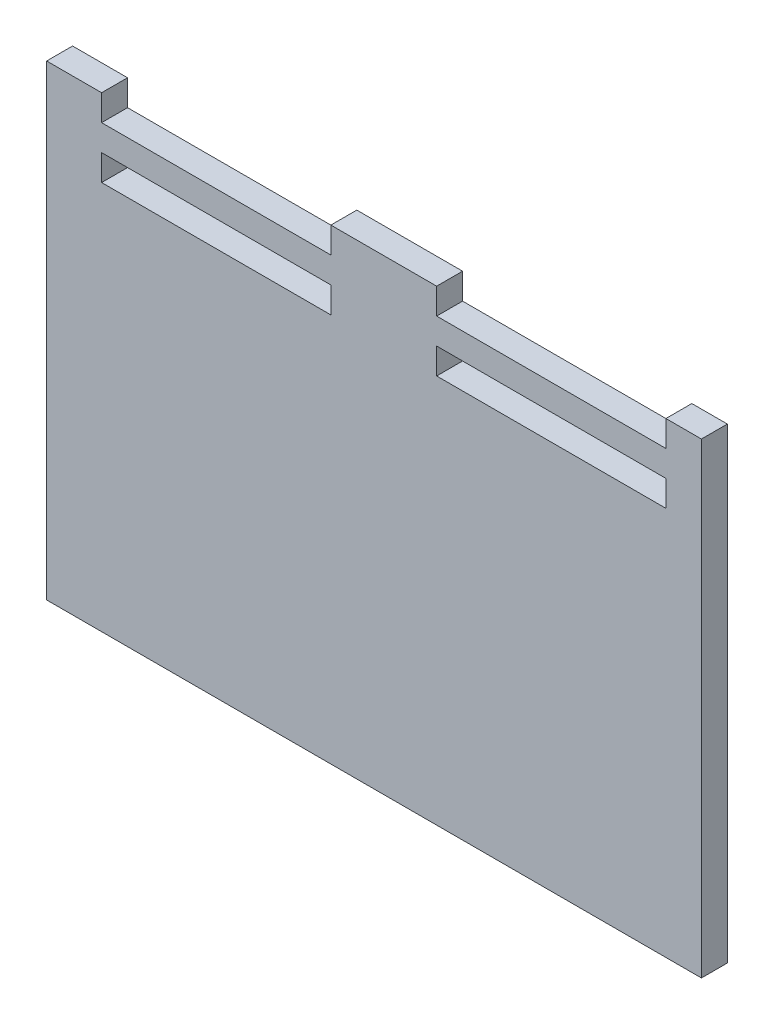
SolidWorks part; units mm, degrees
ref_plane "Front Plane" through (0, 0, 0) normal (0, 0, 1) x (1, 0, 0)
ref_plane "Top Plane" through (0, 0, 0) normal (0, 1, 0) x (1, 0, 0)
ref_plane "Right Plane" through (0, 0, 0) normal (1, 0, 0) x (0, 0, -1)
sketch "Sketch1" plane through (0, 0, 0) normal (0, 0, 1) x (1, 0, 0)
  line L1 (0, 0) -> (304.8, 0)
  line L2 (0, 0) -> (0, 228.6)
  line L3 (0, 228.6) -> (304.8, 228.6)
  line L4 (304.8, 0) -> (304.8, 228.6)
  dimension "D1" = 304.8
  dimension "D2" = 228.6
extrude "Boss-Extrude1" add sketch "Sketch1" along normal blind 12.7
sketch "Sketch6" plane through (0, 0, 12.7) normal (0, 0, 1) x (1, 0, 0)
  line L0 (0, 114.3) -> (304.8, 114.3) construction
  line L1 (0, 228.6) -> (0, 0) construction
  line L2 (304.8, 0) -> (304.8, 228.6) construction
sketch "Sketch7" plane through (0, 0, 12.7) normal (0, 0, 1) x (1, 0, 0)
  line L1 (14.224, 228.6) -> (126.492, 228.6)
  line L2 (14.224, 228.6) -> (14.224, 215.9)
  line L3 (14.224, 215.9) -> (126.492, 215.9)
  line L4 (0, 228.6) -> (0, 0)
  line L5 (0, 0) -> (304.8, 0)
  line L6 (304.8, 0) -> (304.8, 228.6)
  line L7 (304.8, 228.6) -> (0, 228.6)
  line L8 (0, 228.6) -> (0, 0)
  line L9 (0, 0) -> (304.8, 0)
  line L10 (304.8, 0) -> (304.8, 228.6)
  line L11 (304.8, 228.6) -> (0, 228.6)
  line L12 (126.492, 228.6) -> (126.492, 215.9)
  line L13 (178.308, 228.6) -> (290.576, 228.6)
  line L14 (178.308, 228.6) -> (178.308, 215.9)
  line L15 (178.308, 215.9) -> (290.576, 215.9)
  line L16 (290.576, 228.6) -> (290.576, 215.9)
  line L17 (14.224, 203.2) -> (126.492, 203.2)
  line L18 (14.224, 203.2) -> (14.224, 190.5)
  line L19 (14.224, 190.5) -> (126.492, 190.5)
  line L20 (126.492, 203.2) -> (126.492, 190.5)
  line L21 (178.308, 203.2) -> (290.576, 203.2)
  line L22 (178.308, 203.2) -> (178.308, 190.5)
  line L23 (178.308, 190.5) -> (290.576, 190.5)
  line L24 (290.576, 203.2) -> (290.576, 190.5)
  point P20 (70.358, 203.2)
  line M17 (304.8, 228.6) -> (0, 228.6)
  dimension "D2" = 14.224
  dimension "D3" = 112.268
  dimension "D4" = 112.268
  dimension "D5" = 14.224
  dimension "D6" = 12.7
  dimension "D7" = 12.7
  dimension "D8" = 12.7
  dimension "D9" = 112.268
  dimension "D10" = 112.268
  dimension "D11" = 12.7
  dimension "D12" = 12.7
  dimension "D1" = 0
extrude "Cut-Extrude2" cut sketch "Sketch7" against normal blind 12.7 contours L12 L2 L3 M17 | L15 L16 L13 L14 | L18 L17 L20 L19 | L22 L21 L24 L23
sketch "Sketch8" plane through (0, 0, 12.7) normal (0, 0, 1) x (1, 0, 0)
  line L1 (304.8, 228.6) -> (307.975, 228.6)
  line L2 (304.8, 228.6) -> (304.8, 0)
  line L3 (304.8, 0) -> (307.975, 0)
  line L4 (307.975, 228.6) -> (307.975, 0)
  line L5 (0, 228.6) -> (-12.7, 228.6)
  line L6 (0, 228.6) -> (0, 0)
  line L7 (0, 0) -> (-12.7, 0)
  line L8 (-12.7, 228.6) -> (-12.7, 0)
  line L12 (290.576, 215.9) -> (178.308, 215.9)
  line L13 (178.308, 215.9) -> (178.308, 228.6)
  line L14 (178.308, 228.6) -> (126.492, 228.6)
  line L15 (126.492, 228.6) -> (126.492, 215.9)
  line L16 (126.492, 215.9) -> (14.224, 215.9)
  line L17 (14.224, 215.9) -> (14.224, 228.6)
  line L18 (14.224, 228.6) -> (0, 228.6)
  line L19 (0, 228.6) -> (0, 0)
  line L20 (0, 0) -> (304.8, 0)
  line L21 (304.8, 0) -> (304.8, 228.6)
  line L22 (304.8, 228.6) -> (290.576, 228.6)
  line L23 (290.576, 228.6) -> (290.576, 215.9)
  line L24 (290.576, 215.9) -> (178.308, 215.9)
  line L25 (178.308, 215.9) -> (178.308, 228.6)
  line L26 (178.308, 228.6) -> (126.492, 228.6)
  line L27 (126.492, 228.6) -> (126.492, 215.9)
  line L28 (126.492, 215.9) -> (14.224, 215.9)
  line L29 (14.224, 215.9) -> (14.224, 228.6)
  line L30 (14.224, 228.6) -> (0, 228.6)
  line L31 (0, 228.6) -> (0, 0)
  line L32 (0, 0) -> (304.8, 0)
  line L33 (304.8, 0) -> (304.8, 228.6)
  line L34 (304.8, 228.6) -> (290.576, 228.6)
  line L35 (290.576, 228.6) -> (290.576, 215.9)
  line M22 (0, 228.6) -> (0, 0)
  line M24 (304.8, 0) -> (304.8, 228.6)
  dimension "D2" = 12.7
  dimension "D3" = 3.175
  dimension "D1" = 0
extrude "Boss-Extrude2" add sketch "Sketch8" against normal blind 12.7 contours L5 L8 L7 M22 | L4 L1 L3 M24
